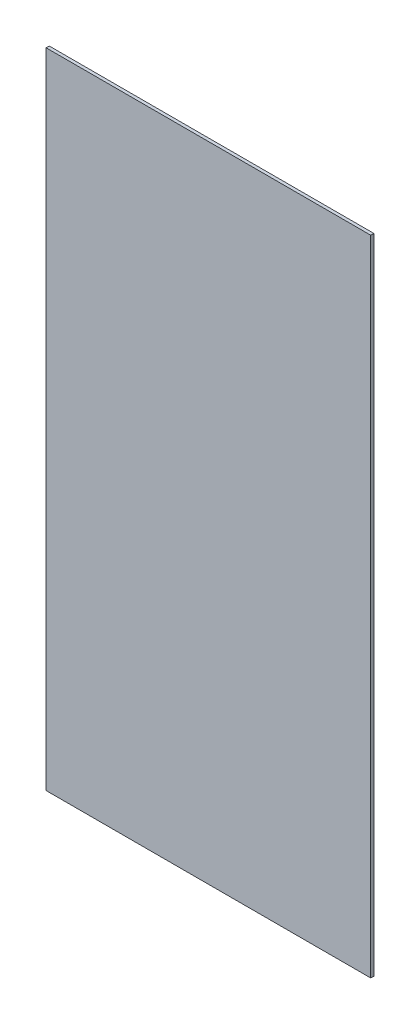
SolidWorks part; units mm, degrees
ref_plane "Plan de face" through (0, 0, 0) normal (0, 0, 1) x (1, 0, 0)
ref_plane "Plan de dessus" through (0, 0, 0) normal (0, 1, 0) x (1, 0, 0)
ref_plane "Plan de droite" through (0, 0, 0) normal (1, 0, 0) x (0, 0, -1)
sketch "Esquisse1" plane through (0, 0, 0) normal (0, 0, 1) x (1, 0, 0)
  line L1 (-408.0273, 376.8615) -> (111.9727, 376.8615)
  line L2 (-408.0273, 376.8615) -> (-408.0273, -653.6385)
  line L3 (-408.0273, -653.6385) -> (111.9727, -653.6385)
  line L4 (111.9727, 376.8615) -> (111.9727, -653.6385)
  dimension "D1" = 1030.5
  dimension "D2" = 520
extrude "Boss.-Extru.1" add sketch "Esquisse1" along normal blind 5
